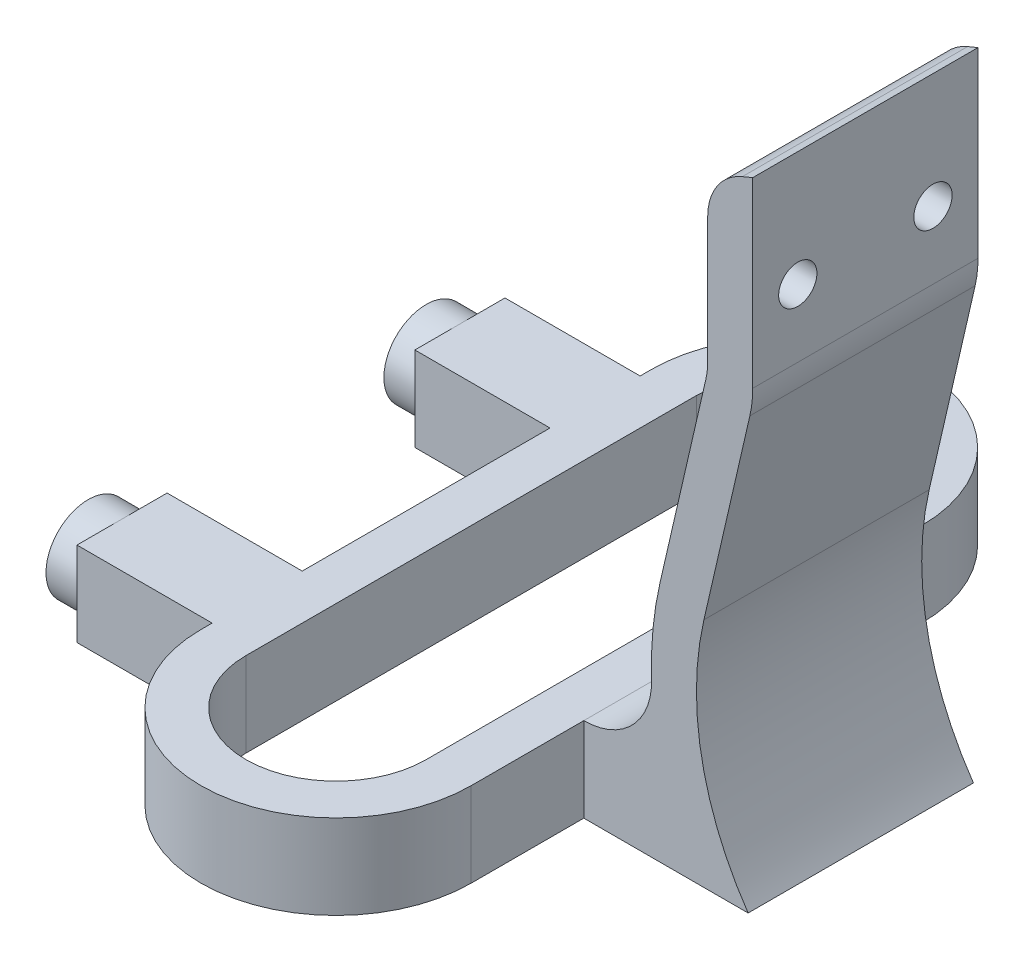
SolidWorks part; units mm, degrees
ref_plane "Front Plane" through (0, 0, 0) normal (0, 0, 1) x (1, 0, 0)
ref_plane "Top Plane" through (0, 0, 0) normal (0, 1, 0) x (1, 0, 0)
ref_plane "Right Plane" through (0, 0, 0) normal (1, 0, 0) x (0, 0, -1)
sketch "Sketch1" plane through (0, 0, 0) normal (0, 1, 0) x (1, 0, 0)
  line L0 (0, -11) -> (12, -11)
  line L1 (12, -11) -> (12, 11)
  line L2 (12, 11) -> (0, 11)
  line L3 (0, 11) -> (0, 19)
  line L4 (0, 19) -> (12, 19)
  line L5 (55, 10) -> (55, -10)
  line L6 (12, 19) -> (12, 20)
  line L7 (0, -19) -> (0, -11)
  line L8 (36, 20) -> (36, 10)
  line L9 (36, 10) -> (55, 10)
  line L10 (0, -19) -> (12, -19)
  line L11 (36, -20) -> (36, -10)
  line L12 (36, -10) -> (55, -10)
  line L13 (12, -19) -> (12, -20)
  line L14 (24, 20) -> (24, -20) construction
  line L15 (32, 20) -> (32, -20)
  line L16 (16, 20) -> (16, -20)
  arc A0 (12, 20) -> (36, 20) centre (24, 20) cw
  arc A1 (12, -20) -> (36, -20) centre (24, -20) ccw
  arc A2 (32, 20) -> (16, 20) centre (24, 20) ccw
  arc A3 (16, -20) -> (32, -20) centre (24, -20) ccw
  point P8 (0, 15)
  point P9 (0, -15)
  point P19 (24, 0)
  dimension "D11" = 12
  dimension "D12" = 4
  dimension "D1" = 55
  dimension "D2" = 8
  dimension "D3" = 8
  dimension "D4" = 30
  dimension "D5" = 11
  dimension "D6" = 20
  dimension "D7" = 20
  dimension "D8" = 10
  dimension "D9" = 20
  dimension "D10" = 12
extrude "Boss-Extrude1" add sketch "Sketch1" along normal mid plane 7.5 contours L2 L3 L4 L6 A0 L8 L9 L5 L12 L11 A1 L13 L10 L7 L0 L1
sketch "Sketch2" plane through (0, 0, 0) normal (-1, 0, 0) x (0, 0, 1)
  line L2 (-11, -3.75) -> (-19, -3.75) construction
  line L4 (-19, 3.75) -> (-19, -3.75) construction
  line L5 (19, 3.75) -> (19, -3.75) construction
  circle A0 centre (-15, 0) radius 3.75
  circle A1 centre (15, 0) radius 3.75
  dimension "D1" = 7.5
  dimension "D2" = 7.5
  dimension "D3" = 4
  dimension "D4" = 4
  dimension "D5" = 3.75
extrude "Boss-Extrude2" add sketch "Sketch2" along normal blind 3
hole_wizard "M4 Clearance Hole1" positions "Sketch3" profile "Sketch4" hole size "M4" standard "ANSI Metric"
sketch "Sketch3" plane through (-3, 0, 0) normal (-1, 0, 0) x (0, 0, 1)
  circle A0 centre (15, 0) radius 3.75 construction
  circle A1 centre (-15, 0) radius 3.75 construction
  point P0 (-15, 0)
  point P2 (15, 0)
sketch "Sketch4" plane through (-3, 0, -15) normal (0, 1, 0) x (0, 0, 1)
  line L0 (0, 0) -> (0, 11.3519)
  line L1 (0, 11.3519) -> (2.25, 10)
  line L2 (2.25, 10) -> (2.25, 0)
  line L5 (2.25, 0) -> (0, 0)
  line L10 (0, 11.3519) -> (-2.25, 10) construction
  line L11 (0, -6.35) -> (0, 107.95) construction
  dimension "Hole Dia." = 4.5
  dimension "Hole Depth" = 10
  dimension "Drill Angle" = 118
sketch "Sketch5" plane through (0, 0, 0) normal (0, 0, 1) x (1, 0, 0)
  line L0 (88, -21) -> (55, -21)
  line L1 (55, -21) -> (55, -10.8403)
  line L2 (46.6628, 16.8333) -> (50.7432, 34.5564)
  line L3 (50.9981, 36.8) -> (50.9981, 61)
  line L4 (50.9981, 61) -> (62.6361, 61)
  line L5 (88, -21) -> (88, -11)
  line L6 (88, -11) -> (72, -11)
  line L7 (-3, 3.75) -> (-3, -3.75) construction
  arc A0 (55, -10.8403) -> (53.5484, -7.3177) centre (50, -10.8403) ccw
  arc A1 (53.5484, -7.3177) -> (46.6628, 16.8333) centre (72, 11) cw
  arc A2 (50.7432, 34.5564) -> (50.9981, 36.8) centre (40.9981, 36.8) ccw
  arc A3 (72, -11) -> (59.8155, -7.3177) centre (72, 11) cw
  dimension "D1" = 10
  dimension "D2" = 5
  dimension "D3" = 26
  dimension "D6" = 22
  dimension "D4" = 33
  dimension "D5" = 16
  dimension "D7" = 10
  dimension "D8" = 82
  dimension "D9" = 167.035
  dimension "D10" = 24.2
  dimension "D11" = 58
  dimension "D12" = 21
sketch "Sketch6" plane through (0, 0, 0) normal (0, 0, 1) x (1, 0, 0)
  line L0 (53.5484, -7.3177) -> (58.5127, -6.4768)
  line L1 (58.5127, -6.4768) -> (58.5127, 16.8333)
  line L2 (58.5127, 16.8333) -> (46.6628, 16.8333)
  arc A0 (46.6628, 16.8333) -> (53.5484, -7.3177) centre (72, 11) ccw
  arc A1 (46.6628, 16.8333) -> (53.5484, -7.3177) centre (72, 11) ccw construction
extrude "Cut-Extrude1" cut sketch "Sketch6" against normal through all both and the other way through all
sketch "Sketch7" plane through (0, 0, 0) normal (0, 0, 1) x (1, 0, 0)
  line L0 (46.6628, 16.8333) -> (50.7432, 34.5564) construction
  line L1 (46.6628, 16.8333) -> (50.7432, 34.5564)
  line L2 (50.9981, 36.8) -> (50.9981, 53)
  line L3 (88, -21) -> (55, -21) construction
  line L4 (50.075, 52.6154) -> (50.9981, 53)
  line L5 (46.9981, 48) -> (46.9981, 36.8)
  line L6 (46.8451, 35.4539) -> (42.7648, 17.7307)
  line L7 (36, 3.75) -> (47.0313, 3.75)
  line L8 (36, 3.75) -> (36, -3.75) construction
  arc A0 (47.0313, 3.75) -> (46.6628, 16.8333) centre (72, 11) cw
  arc A1 (50.7432, 34.5564) -> (50.9981, 36.8) centre (40.9981, 36.8) ccw
  arc A2 (42.7648, 17.7307) -> (42.0175, 9.9764) centre (72, 11) ccw
  arc A3 (46.9981, 36.8) -> (46.8451, 35.4539) centre (40.9981, 36.8) cw
  arc A4 (42.0175, 9.9764) -> (36, 3.75) centre (36, 9.771) cw
  arc A5 (50.075, 52.6154) -> (46.9981, 48) centre (51.9981, 48) ccw
  dimension "D1" = 6
  dimension "D2" = 5
  dimension "D3" = 5
  dimension "D4" = 74
extrude "Boss-Extrude3" add sketch "Sketch7" along normal mid plane 20
hole_wizard "M3 Clearance Hole1" positions "Sketch8" profile "Sketch9" hole size "M3" standard "ANSI Metric"
sketch "Sketch8" plane through (46.9981, 0, 0) normal (-1, 0, 0) x (0, 0, 1)
  line L0 (0, 36.8) -> (0, 61) construction
  line L2 (10, 36.8) -> (-10, 36.8) construction
  point P0 (-6, 42.8)
  point P2 (6, 42.8)
  dimension "D1" = 6
  dimension "D2" = 6
  dimension "D3" = 6
sketch "Sketch9" plane through (46.9981, 42.8, -6) normal (0, 1, 0) x (0, 0, 1)
  line L0 (0, 0) -> (0, 11.0215)
  line L1 (0, 11.0215) -> (1.7, 10)
  line L2 (1.7, 10) -> (1.7, 0)
  line L5 (1.7, 0) -> (0, 0)
  line L10 (0, 11.0215) -> (-1.7, 10) construction
  line L11 (0, -6.35) -> (0, 107.95) construction
  dimension "Hole Dia." = 3.4
  dimension "Hole Depth" = 10
  dimension "Drill Angle" = 118
